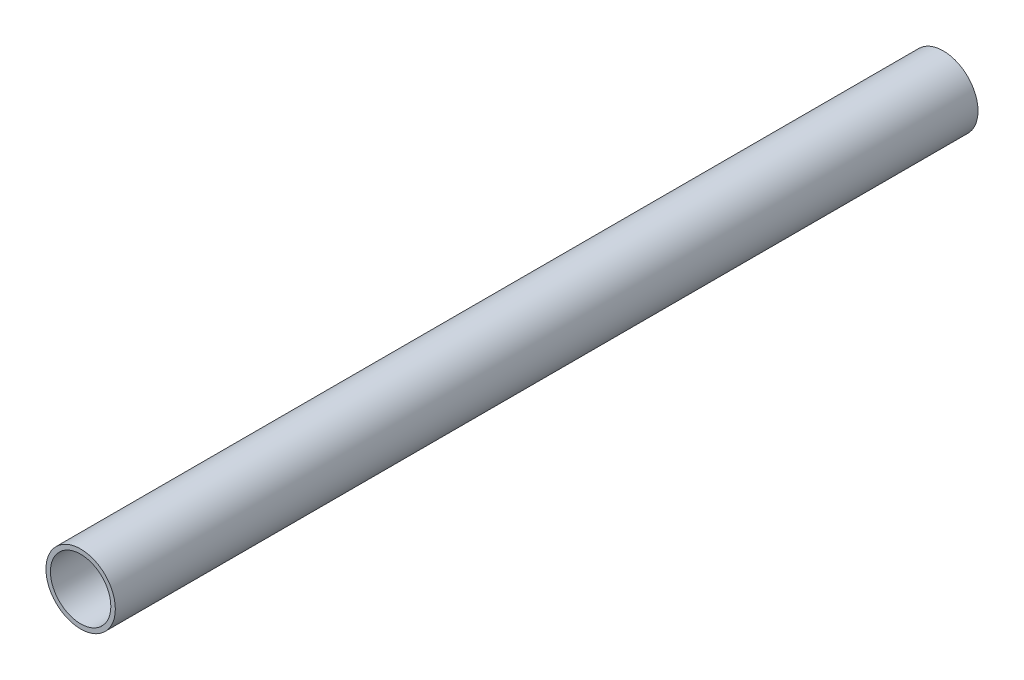
SolidWorks part; units mm, degrees
ref_plane "Front Plane" through (0, 0, 0) normal (0, 0, 1) x (1, 0, 0)
ref_plane "Top Plane" through (0, 0, 0) normal (0, 1, 0) x (1, 0, 0)
ref_plane "Right Plane" through (0, 0, 0) normal (1, 0, 0) x (0, 0, -1)
sketch "Sketch1" plane through (0, 0, 0) normal (0, 0, 1) x (1, 0, 0)
  circle A0 centre (0, 0) radius 30.1625
  dimension "Pipe OD" = 60.325
extrude "Extrude-Thin1" add sketch "Sketch1" along normal mid plane 750 thin thin type one direction reverse wall 3.9116
